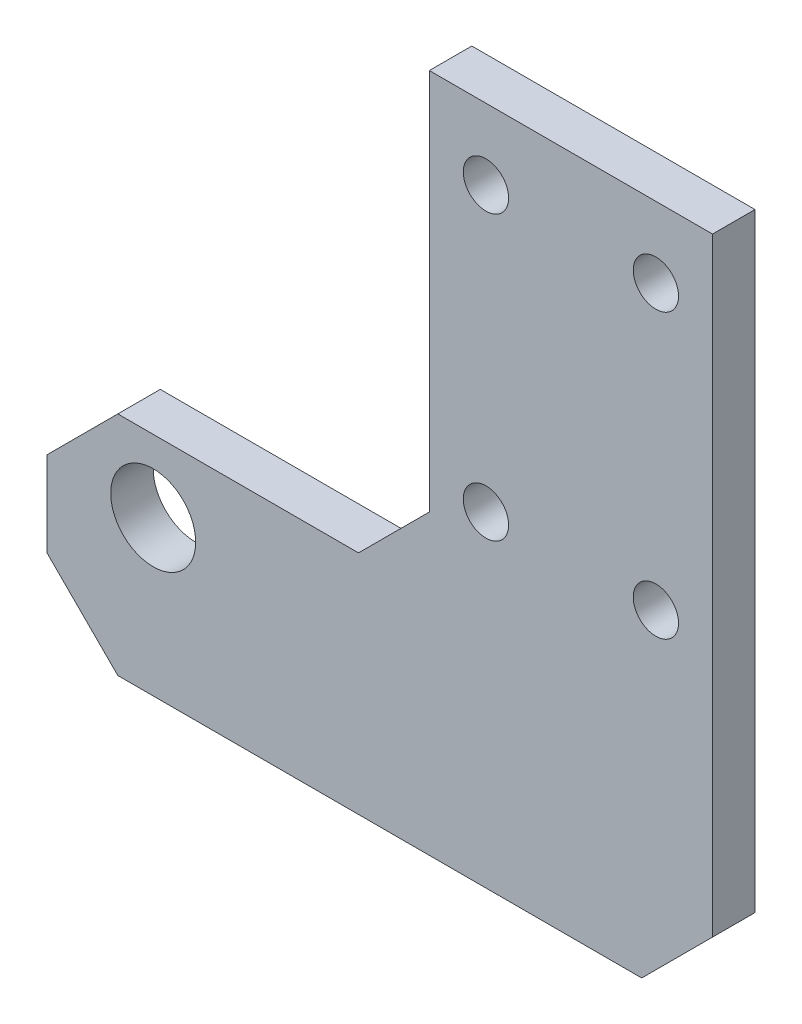
SolidWorks part; units mm, degrees
material "Thornel Mat VMA"
ref_plane "前视基准面" through (0, 0, 0) normal (0, 0, 1) x (1, 0, 0)
ref_plane "上视基准面" through (0, 0, 0) normal (0, 1, 0) x (1, 0, 0)
ref_plane "右视基准面" through (0, 0, 0) normal (1, 0, 0) x (0, 0, -1)
sketch "Sketch1" plane through (0, 0, 0) normal (0, 0, 1) x (1, 0, 0)
  line L0 (330.6121, -180) -> (330.6121, 0) construction
  line L1 (330.6121, -150) -> (350.6121, -150)
  line L2 (330.6121, -150) -> (330.6121, -177)
  line L3 (330.6121, -198) -> (345.6121, -198)
  line L4 (350.6121, -150) -> (350.6121, -193)
  line L5 (350.6121, -180) -> (350.6121, 0) construction
  line L6 (350.6121, -180) -> (330.6121, -180) construction
  line L7 (330.6121, -177) -> (325.6121, -182)
  line L8 (330.6121, -198) -> (308.6121, -198)
  line L10 (325.6121, -182) -> (308.6121, -182)
  line L11 (303.6121, -193) -> (303.6121, -187)
  line L12 (345.6121, -198) -> (350.6121, -193)
  line L13 (308.6121, -198) -> (303.6121, -193)
  line L14 (308.6121, -182) -> (303.6121, -187)
  line L16 (334.6121, -155) -> (346.6121, -155) construction
  line L17 (334.6121, -155) -> (334.6121, -175) construction
  line L18 (334.6121, -175) -> (346.6121, -175) construction
  line L19 (346.6121, -155) -> (346.6121, -175) construction
  circle A0 centre (311.1121, -187.1) radius 3
  circle A1 centre (334.6121, -155) radius 1.6
  circle A2 centre (346.6121, -155) radius 1.6
  circle A3 centre (334.6121, -175) radius 1.6
  circle A4 centre (346.6121, -175) radius 1.6
  point P1 (350.6121, -198)
  point P10 (303.6121, -182)
  point P11 (330.6121, -182)
  point P12 (303.6121, -198)
  dimension "D6" = 5.1
  dimension "D10" = 6
  dimension "D16" = 3.2
  dimension "D1" = 30
  dimension "D2" = 18
  dimension "D3" = 16
  dimension "D4" = 27
  dimension "D5" = 7.5
  dimension "D11" = 4
  dimension "D12" = 4
  dimension "D14" = 5
  dimension "D15" = 5
extrude "Boss-Extrude1" add sketch "Sketch1" along normal blind 3
